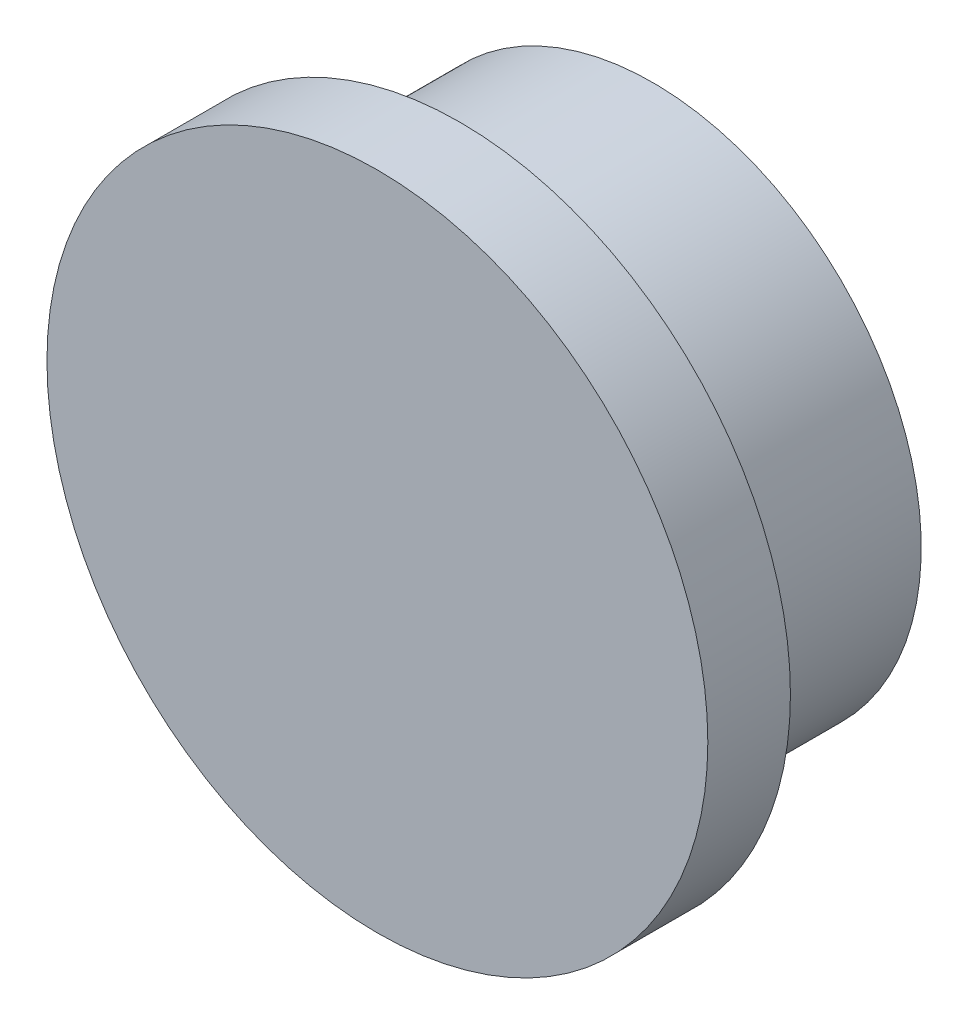
SolidWorks part; units mm, degrees
ref_plane "Front Plane" through (0, 0, 0) normal (0, 0, 1) x (1, 0, 0)
ref_plane "Top Plane" through (0, 0, 0) normal (0, 1, 0) x (1, 0, 0)
ref_plane "Right Plane" through (0, 0, 0) normal (1, 0, 0) x (0, 0, -1)
sketch "Sketch1" plane through (0, 0, 0) normal (0, 0, 1) x (1, 0, 0)
  circle A0 centre (-127.9925, 40.1033) radius 12
extrude "Boss-Extrude1" add sketch "Sketch1" along normal blind 3
sketch "Sketch2" plane through (0, 0, 0) normal (0, 0, -1) x (-1, 0, 0)
  circle A1 centre (127.9925, 40.1033) radius 9.75
extrude "Boss-Extrude2" add sketch "Sketch2" along normal blind 7
sketch "Sketch3" plane through (0, 0, -7) normal (0, 0, -1) x (-1, 0, 0)
  circle A1 centre (127.9925, 40.1033) radius 2.35
extrude "Cut-Extrude1" cut sketch "Sketch3" against normal blind 5
